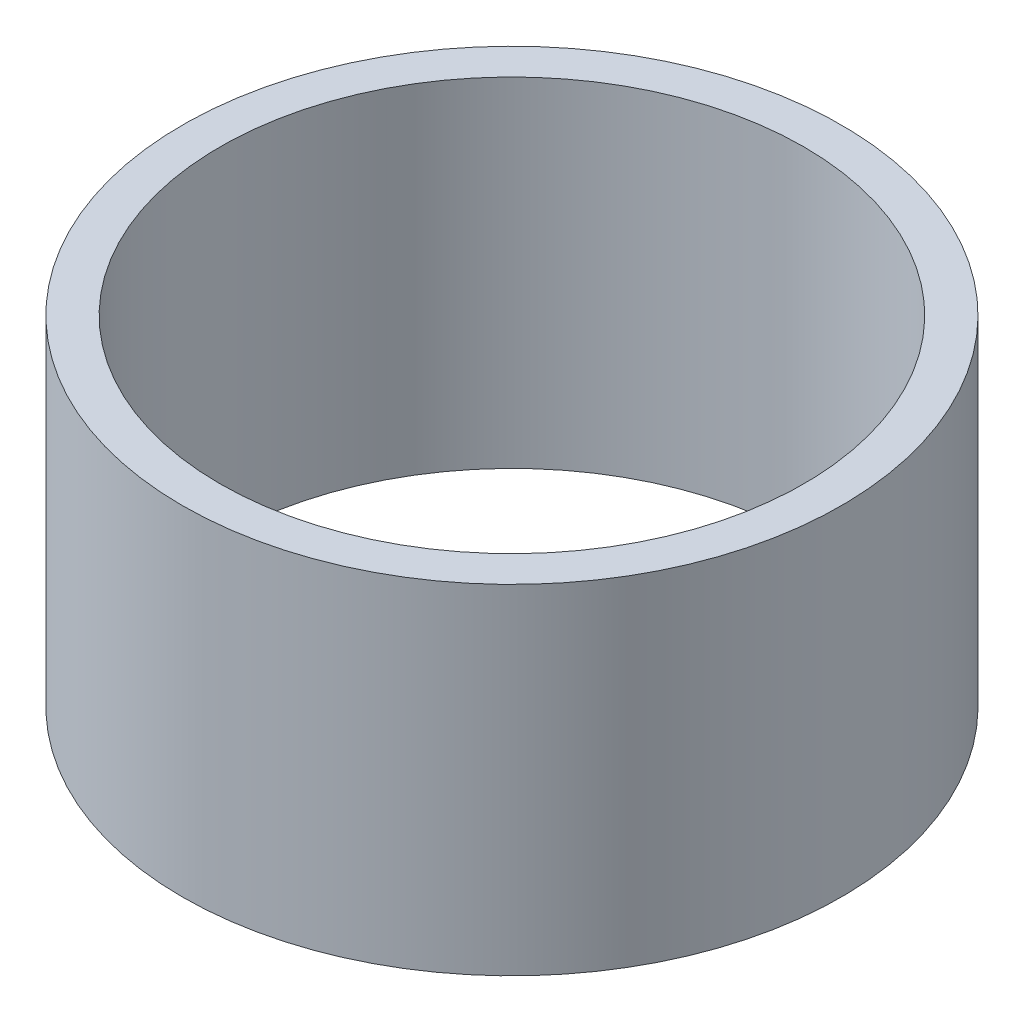
SolidWorks part; units mm, degrees
ref_plane "Front Plane" through (0, 0, 0) normal (0, 0, 1) x (1, 0, 0)
ref_plane "Top Plane" through (0, 0, 0) normal (0, 1, 0) x (1, 0, 0)
ref_plane "Right Plane" through (0, 0, 0) normal (1, 0, 0) x (0, 0, -1)
sketch "Sketch1" plane through (0, 0, 0) normal (0, 1, 0) x (1, 0, 0)
  circle A0 centre (0, 0) radius 17.5
  dimension "D1" = 35
extrude "Boss-Extrude1" add sketch "Sketch1" along normal blind 18
sketch "Sketch2" plane through (0, 18, 0) normal (0, 1, 0) x (1, 0, 0)
  circle A0 centre (0, 0) radius 15.5
  circle A1 centre (0, 0) radius 17.5 construction
  dimension "D1" = 2
extrude "Cut-Extrude1" cut sketch "Sketch2" against normal up to surface (18 mm away) up to face at (0, 0, 17.5)
